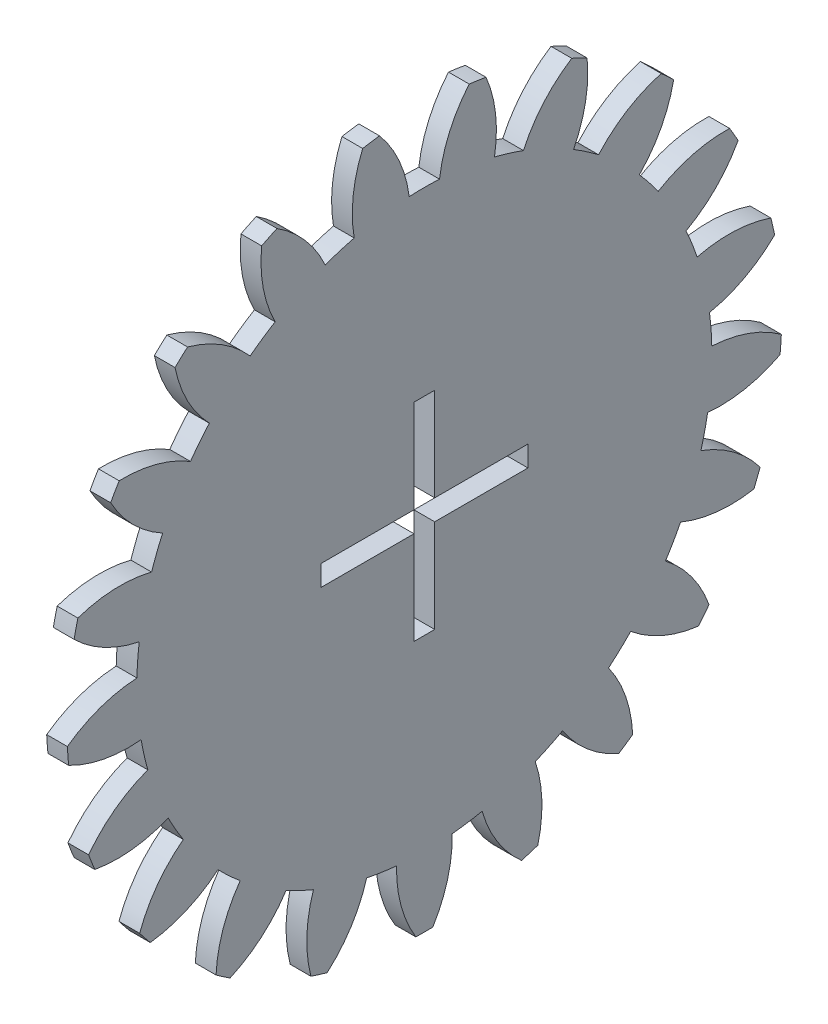
SolidWorks part; units mm, degrees
ref_plane "Plane1" through (0, 0, 0) normal (0, 0, 1) x (1, 0, 0)
ref_plane "Plane2" through (0, 0, 0) normal (0, 1, 0) x (1, 0, 0)
ref_plane "Plane3" through (0, 0, 0) normal (1, 0, 0) x (0, 0, -1)
sketch "HoldingSke" plane through (0, 0, 0) normal (0, 1, 0) x (1, 0, 0)
  line L0 (0, 0) -> (0.2075, -0.0796)
  line L1 (-15, 0) -> (100, 0) construction
  line L2 (0, 0) -> (-2.1039, 2.3779)
  line L3 (0, 0) -> (-11.863, 4.5341)
  line L4 (0, 0) -> (8.0624, 3.0949)
  line L5 (0, 0) -> (-46.8476, -17.4728)
  line L6 (0, 0) -> (-2.4869, -1.6779)
  line L7 (-2.1039, 2.3779) -> (8.6586, 51.2059)
  line L8 (-76.2, 54.61) -> (-76.1, 54.61)
  line L9 (-71.009, 38.7566) -> (-53.1078, 45.2721)
  line L10 (-76.2, 71.12) -> (104.1128, 71.12)
  line L11 (0, 0) -> (-3, 0)
  line L12 (-76.2, 101.6) -> (-76.053, 101.6)
  line L13 (24.9733, 27.94) -> (52.9518, 28.4284)
  line L14 (24.9733, 27.94) -> (24.9743, 27.94)
  line L15 (24.9733, 27.94) -> (100.4006, 29.5858)
  line L16 (-63.627, -4.5) -> (-12.827, -4.5)
  circle A0 centre (0, 0) radius 0.45
  circle A1 centre (0, 0) radius 37.5
  circle A2 centre (0, 0) radius 37.5
  circle A3 centre (0, 0) radius 0.45
  dimension "MHD" = 75
  dimension "Hub_dia" = 75
  dimension "Bore" = 0.9
  dimension "MBD" = 0.9
  dimension "Num_teeth" = 21
  dimension "Pitch" = 0.2222
  dimension "Overall_len" = 50
  dimension "Show_teeth" = 21
  dimension "Thickness" = 3
  dimension "OAL" = 50.0001
  dimension "T_dim" = 0.1
  dimension "Ap" = 20
  dimension "H" = 19.05
  dimension "Pitch_radius" = 180.3128
  dimension "Width" = 3
  dimension "Backlash" = 0.147
  dimension "Addendum_fac" = 1
  dimension "Dedendum_fac" = 1.25
  dimension "Clearance_fac" = 0.25
  dimension "Dedendum_add" = 0.001
  dimension "Module" = 4.5
sketch "BasProSke" plane through (0, 0, 0) normal (0, 1, 0) x (1, 0, 0)
  line L0 (-10, 0) -> (60, 0) construction
  line L1 (0, 0) -> (0, 51.75)
  line L2 (0, 0) -> (3, 0)
  line L3 (3, 0) -> (3, 51.75)
  line L4 (3, 51.75) -> (0, 51.75)
  dimension "Thickness" = 3
  dimension "Diameter" = 103.5
revolve "Base-Revolve" add sketch "BasProSke" angle 360 about L0
sketch "TooCutSke" plane through (0, 0, 0) normal (1, 0, 0) x (0, 0, -1)
  line L1 (0, 0) -> (0, 107) construction
  line L2 (0, 0) -> (-3.7881, 47.0979) construction
  line L3 (0, 0) -> (-14.0506, 93.22) construction
  line L4 (-3.7881, 47.0979) -> (-7.0253, 46.61) construction
  arc A0 (2.1921, 41.5662) -> (-2.1921, 41.5662) centre (0, 0) ccw
  arc A1 (6.5114, 51.3643) -> (-6.5114, 51.3643) centre (0, 0) ccw
  circle A2 centre (0, 0) radius 47.25 construction
  circle A3 centre (0, 0) radius 44.4005 construction
  arc A4 (-2.1921, 41.5662) -> (-6.5114, 51.3643) centre (-20.9375, 39.1538) ccw
  arc A5 (6.5114, 51.3643) -> (2.1921, 41.5662) centre (20.9375, 39.1538) ccw
  dimension "Root_dia" = 83.248
  dimension "Overcut_dia" = 103.5508
  dimension "Pitch_dia" = 94.5
  dimension "Base_dia" = 88.801
  dimension "Flank_rad" = 18.9
  dimension "Half_ang" = 8.571
  dimension "Half_CT" = 3.2737
extrude "ToothCut" cut sketch "TooCutSke" along normal through all
fillet "Breaks" [suppressed] radius 0.09
fillet "RootFillets" [suppressed] radius 1.126
pattern_circular "TeethCuts" count 21 every 17.143 about axis through (-10, 0, 0) along (1, 0, 0) of "ToothCut", "RootFillets", "Breaks"
sketch "HubNeaOneSke" plane through (0, 0, 0) normal (-1, 0, 0) x (0, 0, 1)
  circle A0 centre (0, 0) radius 37.5
  dimension "Diameter" = 75
extrude "HubNearOne" [suppressed] add sketch "HubNeaOneSke" along normal blind 47.0001
sketch "HubNeaBotSke" plane through (0, 0, 0) normal (-1, 0, 0) x (0, 0, 1)
  circle A0 centre (0, 0) radius 37.5
  dimension "Diameter" = 75
extrude "HubNearBoth" [suppressed] add sketch "HubNeaBotSke" along normal blind 23.5
ref_plane "FarPln" through (3, 0, 0) normal (1, 0, 0) x (0, 0, -1)
sketch "HubFarSke" plane through (3, 0, 0) normal (1, 0, 0) x (0, 0, -1)
  circle A0 centre (0, 0) radius 37.5
  dimension "Diameter" = 75
extrude "HubFar" [suppressed] add sketch "HubFarSke" along normal blind 23.5
sketch "BorSke" plane through (0, 0, 0) normal (1, 0, 0) x (0, 0, -1)
  circle A0 centre (0, 0) radius 0.45
  dimension "Diameter" = 0.9
extrude "Bore" cut sketch "BorSke" along normal mid plane 100.0001
sketch "KeySke" plane through (0, 0, 0) normal (1, 0, 0) x (0, 0, -1)
  line L0 (-0.05, 0) -> (-0.05, 0.55)
  line L1 (-0.05, 0.55) -> (0.05, 0.55)
  line L2 (0.05, 0.55) -> (0.05, 0)
  line L3 (0, 0) -> (0, 34) construction
  line L4 (-0.05, 0) -> (0.05, 0)
  dimension "Offset" = 0.55
  dimension "Width" = 0.1
extrude "Keyway" [suppressed] cut sketch "KeySke" along normal mid plane 100.0001
pattern_circular "Keyway2" [suppressed] count 2 every 90 about axis through (-10, 0, 0) along (1, 0, 0)
sketch "Sketch1" plane through (3, 0, 0) normal (1, 0, 0) x (0, 0, -1)
  line L0 (1.5, 1.95) -> (15, 1.95)
  line L1 (-1.5, 15.45) -> (1.5, 15.45)
  line L2 (-1.5, 15.45) -> (-1.5, 1.95)
  line L3 (-1.5, -14.55) -> (1.5, -14.55)
  line L4 (1.5, 15.45) -> (1.5, 1.95)
  line L7 (-15, -1.05) -> (-1.5, -1.05)
  line L8 (-15, -1.05) -> (-15, 1.95)
  line L9 (-15, 1.95) -> (-1.5, 1.95)
  line L10 (15, -1.05) -> (15, 1.95)
  line L11 (1.5, -1.05) -> (1.5, -14.55)
  line L12 (1.5, -1.05) -> (15, -1.05)
  line L13 (-1.5, -1.05) -> (-1.5, -14.55)
  circle A0 centre (0, 0) radius 0.45 construction
  point P0 (0, 0.45)
  point P7 (0, 0.45)
  dimension "D1" = 30
  dimension "D2" = 30
  dimension "D3" = 3
  dimension "D4" = 3
extrude "Cut-Extrude1" cut sketch "Sketch1" against normal through all contours L2 L9 L8 L7 L13 L3 L11 L12 L10 L0 L4 L1
equation "' \"Module@HoldingSke\" = 6.35"
equation "' \"Num_teeth@HoldingSke\" = 12"
equation "' \"Ap@HoldingSke\" =  20"
equation "' \"Ap@HoldingSke\" = 20"
equation "' \"Width@HoldingSke\" = 0.5 * 25.4"
equation "' \"Hub_dia@HoldingSke\"= 1 * 25.4"
equation "' \"Hub_dia@HoldingSke\" = 1 * 25.4"
equation "' \"Overall_len@HoldingSke\" = 1.0 * 25.4"
equation "' \"Bore@HoldingSke\" = 0.75 * 25.4"
equation "' \"T_dim@HoldingSke\" = 0.1 * 25.4"
equation "' \"Width@KeySke\" = 0.25 * 25.4"
equation "' \"Show_teeth@HoldingSke\" = 13"
equation "' \"Backlash@HoldingSke\" = 0.009 * 25.4"
equation "' \"Addendum_fac@HoldingSke\" = 1.0"
equation "' \"Dedendum_fac@HoldingSke\" = 1.25"
equation "' \"Dedendum_add@HoldingSke\" = 0.00005 * 25.4"
equation "' \"Clearance_fac@HoldingSke\" = 0.25"
equation "\"Pitch@HoldingSke\" = 1 / \"Module@HoldingSke\""
equation "\"Overcut_dia@TooCutSke\" = (\"Num_teeth@HoldingSke\" + 2 * \"Addendum_fac@HoldingSke\") / \"Pitch@HoldingSke\" + 0.002 * 25.4"
equation "\"Pitch_dia@TooCutSke\" = \"Num_teeth@HoldingSke\" / \"Pitch@HoldingSke\""
equation "\"Base_dia@TooCutSke\" = \"Num_teeth@HoldingSke\" / \"Pitch@HoldingSke\" * cos((\"Ap@HoldingSke\"  * 3.14159265 / 180))"
equation "\"Root_dia@TooCutSke\" = (\"Num_teeth@HoldingSke\" + 2) / \"Pitch@HoldingSke\" - 2 * (\"Addendum_fac@HoldingSke\" + \"Dedendum_fac@HoldingSke\") / \"Pitch@HoldingSke\" - \"Dedendum_add@HoldingSke\" * 2"
equation "\"Half_ang@TooCutSke\" = 180 / \"Num_teeth@HoldingSke\""
equation "\"Half_CT@TooCutSke\" = \"Num_teeth@HoldingSke\" / \"Pitch@HoldingSke\" * sin((3.14159265 / 2 / \"Num_teeth@HoldingSke\")) / 2 - 7 * \"Backlash@HoldingSke\" / 4"
equation "\"Flank_rad@TooCutSke\" = \"Num_teeth@HoldingSke\" / \"Pitch@HoldingSke\" / 5"
equation "\"Radius@RootFillets\" = \"Clearance_fac@HoldingSke\" / \"Pitch@HoldingSke\" + \"Dedendum_add@HoldingSke\""
equation "\"Break_rad@Breaks\" = 0.02 / \"Pitch@HoldingSke\""
equation "\"Thickness@HoldingSke\" = \"Width@HoldingSke\""
equation "\"OAL@HoldingSke\" = \"Thickness@HoldingSke\""
equation "\"MHD@HoldingSke\" = (\"Num_teeth@HoldingSke\" + 2) / \"Pitch@HoldingSke\" - 2 * (\"Addendum_fac@HoldingSke\" + \"Dedendum_fac@HoldingSke\")  / \"Pitch@HoldingSke\" - \"Dedendum_add@HoldingSke\" * 2"
equation "\"MBD@HoldingSke\" = (\"Num_teeth@HoldingSke\" + 2) / \"Pitch@HoldingSke\" - 2 * (\"Addendum_fac@HoldingSke\" + \"Dedendum_fac@HoldingSke\")  / \"Pitch@HoldingSke\" - \"Dedendum_add@HoldingSke\" * 2 - 0.002 * 25.4"
equation "\"MHD@HoldingSke\" = ((sgn( \"MHD@HoldingSke\" - \"Hub_dia@HoldingSke\" )-1)*( \"MHD@HoldingSke\" - \"Hub_dia@HoldingSke\" ))/-2+ \"Hub_dia@HoldingSke\""
equation "\"MBD@HoldingSke\" = ((sgn( \"MBD@HoldingSke\" - \"Bore@HoldingSke\" )-1)*( \"MBD@HoldingSke\" - \"Bore@HoldingSke\" ))/-2+ \"Bore@HoldingSke\""
equation "\"OAL@HoldingSke\" = ((sgn( \"OAL@HoldingSke\" - \"Overall_len@HoldingSke\" )+1)*( \"OAL@HoldingSke\" - \"Overall_len@HoldingSke\" ))/2 + \"Overall_len@HoldingSke\" + 0.000002 * 25.4"
equation "\"Num_teeth@TeethCuts\" = int( \"Show_teeth@HoldingSke\" ) + 1"
equation "\"Num_teeth@TeethCuts\" = ((sgn( \"Num_teeth@TeethCuts\" - \"Num_teeth@HoldingSke\" )-1)*( \"Num_teeth@TeethCuts\" - \"Num_teeth@HoldingSke\" ))/-2+ \"Num_teeth@HoldingSke\""
equation "\"Num_teeth@TeethCuts\" = ((sgn( \"Num_teeth@TeethCuts\" - 2.0)+1)*( \"Num_teeth@TeethCuts\" - 2.0))/2 +2.0"
equation "\"Angle@TeethCuts\" = 360.0 / \"Num_teeth@HoldingSke\""
equation "\"Diameter@BasProSke\" = (\"Num_teeth@HoldingSke\" + 2 * \"Addendum_fac@HoldingSke\") / \"Pitch@HoldingSke\""
equation "\"Thickness@BasProSke\"  = \"Thickness@HoldingSke\""
equation "' \"Fillet_rad@BasProSke\" =  \"Thickness@HoldingSke\" * 0.05"
equation "' \"Fillet_rad@BasProSke\" = \"Thickness@HoldingSke\" * 0.05"
equation "\"MHD@HoldingSke\" = ((sgn( \"MHD@HoldingSke\" - \"Root_dia@TooCutSke\" )-1)*( \"MHD@HoldingSke\" - \"Root_dia@TooCutSke\" ))/-2+ \"Root_dia@TooCutSke\""
equation "\"Diameter@HubNeaOneSke\" = \"MHD@HoldingSke\""
equation "\"Length@HubNearOne\" = \"OAL@HoldingSke\" - \"Thickness@BasProSke\""
equation "\"Diameter@HubNeaBotSke\" = \"MHD@HoldingSke\""
equation "\"Length@HubNearBoth\" = ( \"OAL@HoldingSke\" - \"Thickness@BasProSke\" ) / 2.0"
equation "\"Thickness@FarPln\" = \"Thickness@BasProSke\""
equation "\"Diameter@HubFarSke\" = \"MHD@HoldingSke\""
equation "\"Length@HubFar\" = ( \"OAL@HoldingSke\" - \"Thickness@BasProSke\" ) / 2.0"
equation "\"Diameter@BorSke\" = \"MBD@HoldingSke\""
equation "\"D1@Bore\" = \"OAL@HoldingSke\" * 2.0"
equation "\"D1@Keyway\" = \"OAL@HoldingSke\" * 2.0"
equation "\"Offset@KeySke\" = \"T_dim@HoldingSke\" + \"MBD@HoldingSke\" / 2.0"
